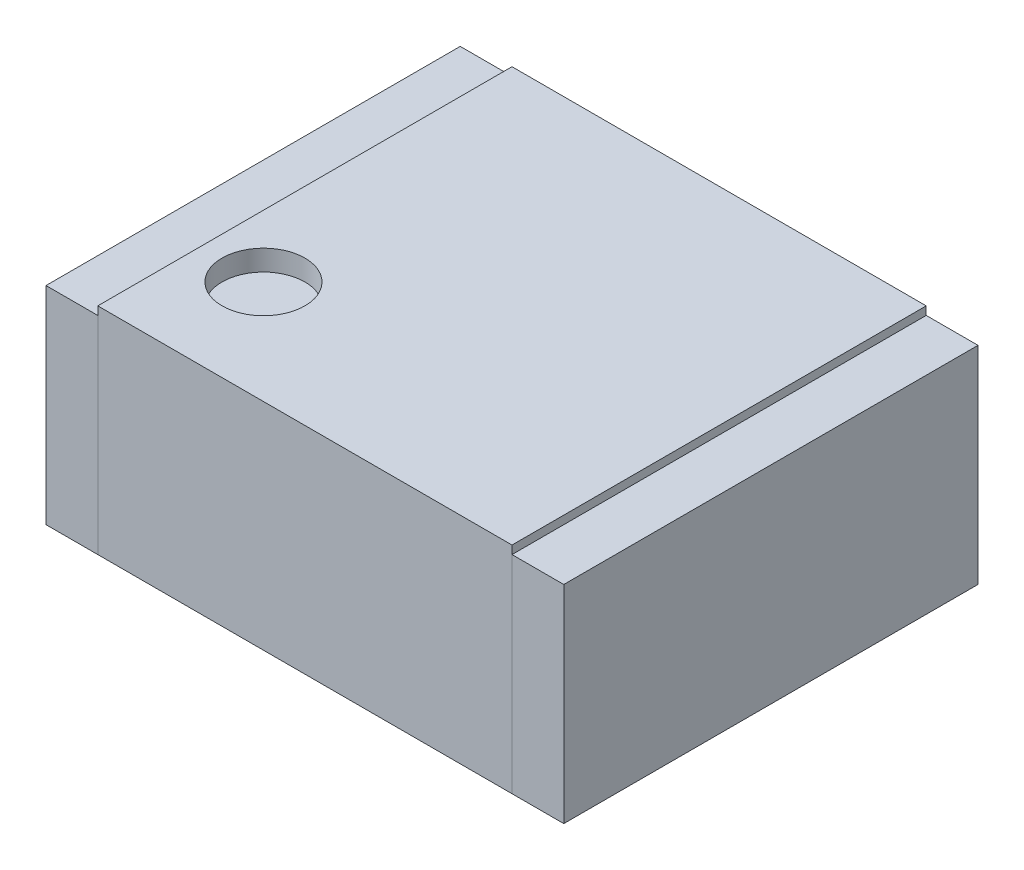
SolidWorks part; units mm, degrees
ref_plane "Front Plane" through (0, 0, 0) normal (0, 0, 1) x (1, 0, 0)
ref_plane "Top Plane" through (0, 0, 0) normal (0, 1, 0) x (1, 0, 0)
ref_plane "Right Plane" through (0, 0, 0) normal (1, 0, 0) x (0, 0, -1)
sketch "Sketch1" plane through (0, 0, 0) normal (0, 1, 0) x (1, 0, 0)
  line L1 (-1, -1) -> (1, -1)
  line L2 (-1, -1) -> (-1, 1)
  line L3 (-1, 1) -> (1, 1)
  line L4 (1, -1) -> (1, 1)
  line L5 (-1, -1) -> (1, 1) construction
  line L6 (-1, 1) -> (1, -1) construction
  point P0 (0, 0)
  dimension "D1" = 2
  dimension "D2" = 2
extrude "Boss-Extrude1" add sketch "Sketch1" along normal blind 1.04
sketch "Sketch3" plane through (0, 0, 0) normal (0, 1, 0) x (1, 0, 0)
  line L0 (0, 1) -> (0, -1) construction
  line L1 (-1, 1) -> (-1.25, 1)
  line L2 (-1, 1) -> (-1, -1)
  line L3 (-1, -1) -> (-1.25, -1)
  line L4 (-1.25, 1) -> (-1.25, -1)
  line L5 (1, 1) -> (-1, 1) construction
  line L6 (-1, -1) -> (1, -1) construction
  line L7 (1, -1) -> (1.25, -1)
  line L8 (1.25, 1) -> (1.25, -1)
  line L9 (1, 1) -> (1.25, 1)
  line L10 (1, 1) -> (1, -1)
  dimension "D1" = 2
  dimension "D2" = 0.25
extrude "Boss-Extrude2" add sketch "Sketch3" along normal blind 1 separate body
sketch "Sketch4" plane through (0, 1.04, 0) normal (0, 1, 0) x (1, 0, 0)
  line L0 (-1, 1) -> (-1, -1) construction
  line L1 (-1, -1) -> (1, -1) construction
  circle A0 centre (-0.7, -0.5) radius 0.2
  dimension "D1" = 0.3
  dimension "D2" = 0.5
  dimension "D3" = 0.4
extrude "Cut-Extrude1" cut sketch "Sketch4" against normal blind 0.1
sketch "Sketch5" plane through (0, 0, 0) normal (0, -1, 0) x (1, 0, 0)
  line L0 (0, 1) -> (0, -1) construction
  line L1 (-1, 1) -> (1, 1) construction
  line L2 (1, -1) -> (-1, -1) construction
  line L3 (-1, 0) -> (1, 0) construction
  line L4 (-1, 1) -> (-1, -1) construction
  line L5 (1, -1) -> (1, 1) construction
  line L6 (-0.75, 0.45) -> (-0.65, 0.55)
  line L7 (-0.75, -0.55) -> (0.75, -0.55)
  line L8 (-0.75, -0.55) -> (-0.75, 0.45)
  line L9 (-0.65, 0.55) -> (0.75, 0.55)
  line L10 (0.75, -0.55) -> (0.75, 0.55)
  line L11 (-0.75, -0.55) -> (0.75, 0.55) construction
  line L12 (-0.75, 0.55) -> (0.75, -0.55) construction
  line L13 (0.4, -0.95) -> (0.4, -0.75)
  line L14 (-0.15, -0.95) -> (0.15, -0.95)
  line L15 (-0.15, -0.95) -> (-0.15, -0.75)
  line L16 (-0.15, -0.75) -> (0.15, -0.75)
  line L17 (0.15, -0.95) -> (0.15, -0.75)
  line L18 (-0.15, -0.95) -> (0.15, -0.75) construction
  line L19 (-0.15, -0.75) -> (0.15, -0.95) construction
  line L20 (0.4, -0.95) -> (0.7, -0.95)
  line L21 (0.7, -0.95) -> (0.7, -0.75)
  line L22 (0.4, -0.75) -> (0.7, -0.75)
  line L23 (-0.7, -0.95) -> (-0.7, -0.75)
  line L24 (-0.7, -0.95) -> (-0.4, -0.95)
  line L25 (-0.4, -0.95) -> (-0.4, -0.75)
  line L26 (-0.7, -0.75) -> (-0.4, -0.75)
  line L27 (-0.15, 0.75) -> (0.15, 0.95) construction
  line L28 (-0.15, 0.95) -> (0.15, 0.75) construction
  line L29 (-0.7, 0.75) -> (-0.4, 0.75)
  line L30 (-0.4, 0.95) -> (-0.4, 0.75)
  line L31 (-0.7, 0.95) -> (-0.4, 0.95)
  line L32 (-0.7, 0.95) -> (-0.7, 0.75)
  line L33 (0.4, 0.75) -> (0.7, 0.75)
  line L34 (0.7, 0.95) -> (0.7, 0.75)
  line L35 (0.4, 0.95) -> (0.7, 0.95)
  line L36 (0.15, 0.95) -> (0.15, 0.75)
  line L37 (-0.15, 0.75) -> (0.15, 0.75)
  line L38 (-0.15, 0.95) -> (-0.15, 0.75)
  line L39 (-0.15, 0.95) -> (0.15, 0.95)
  line L40 (0.4, 0.95) -> (0.4, 0.75)
  point P12 (0, 0)
  point P20 (0, -0.85)
  point P45 (0, 0.85)
  dimension "D1" = 1.1
  dimension "D2" = 1.5
  dimension "D3" = 0.3
  dimension "D4" = 0.2
  dimension "D6" = 0.2
  dimension "D9" = 0.25
  dimension "D10" = 0.25
  dimension "D7" = 2
  dimension "D8" = 2
extrude "Boss-Extrude3" add sketch "Sketch5" against normal blind 0.1 from offset 0.01 separate body
